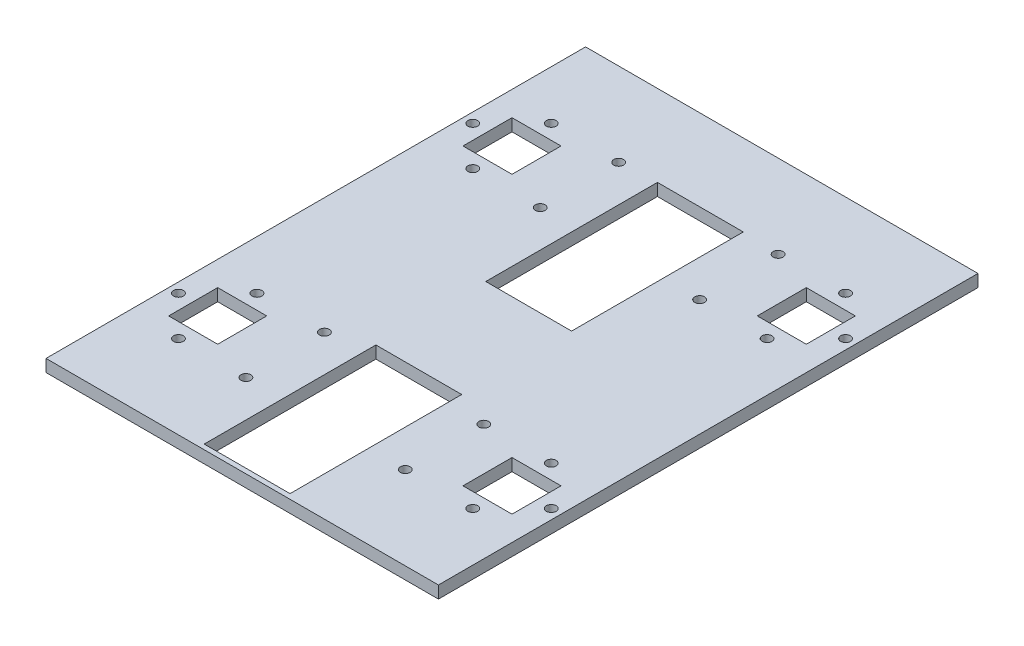
SolidWorks part; units mm, degrees
other "Markup1"
sketch "Sketch4" plane through (-101.6, 6.35, 139.7) normal (-0.0746, 0.7649, 0.6399) x (0.9963, 0.0292, 0.0813)
material "Balsa"
ref_plane "Front Plane" through (0, 0, 0) normal (0, 0, 1) x (1, 0, 0)
ref_plane "Top Plane" through (0, 0, 0) normal (0, 1, 0) x (1, 0, 0)
ref_plane "Right Plane" through (0, 0, 0) normal (1, 0, 0) x (0, 0, -1)
sketch "Sketch1" plane through (0, 0, 0) normal (0, 1, 0) x (1, 0, 0)
  line L1 (-101.6, 139.7) -> (101.6, 139.7)
  line L2 (-101.6, 139.7) -> (-101.6, -139.7)
  line L3 (-101.6, -139.7) -> (101.6, -139.7)
  line L4 (101.6, 139.7) -> (101.6, -139.7)
  line L5 (-101.6, 139.7) -> (101.6, -139.7) construction
  line L6 (-101.6, -139.7) -> (101.6, 139.7) construction
  point P0 (0, 0)
  dimension "D1" = 279.4
  dimension "D2" = 203.2
extrude "Boss-Extrude1" add sketch "Sketch1" along normal blind 6.35
sketch "Sketch2" plane through (0, 6.35, 0) normal (0, 1, 0) x (1, 0, 0)
  line L0 (-101.6, 139.7) -> (-101.6, -139.7) construction
  line L1 (-88.9, 88.9) -> (-63.5, 88.9)
  line L2 (-88.9, 88.9) -> (-88.9, 63.5)
  line L3 (-88.9, 63.5) -> (-63.5, 63.5)
  line L4 (-63.5, 88.9) -> (-63.5, 63.5)
  line L5 (-88.9, 88.9) -> (-63.5, 63.5) construction
  line L6 (-88.9, 63.5) -> (-63.5, 88.9) construction
  line L7 (101.6, 139.7) -> (-101.6, 139.7) construction
  line L8 (-76.2, 76.2) -> (-31.4633, 76.2) construction
  line L9 (-76.2, 55.88) -> (-7.5803, 55.88) construction
  line L10 (-76.2, 76.2) -> (-76.2, 32.693) construction
  circle A4 centre (-41.275, 55.88) radius 2.54
  circle A5 centre (-41.275, 96.52) radius 2.54
  circle A6 centre (-76.2, 55.88) radius 2.54
  circle A7 centre (-96.52, 76.2) radius 2.54
  circle A8 centre (-76.2, 96.52) radius 2.54
  circle A9 centre (-55.88, 76.2) radius 2.54 [skipped]
  point P0 (-76.2, 76.2)
  point P22 (-76.2, 76.2)
  point P30 (-76.2, 76.2)
  dimension "D4" = 5.08
  dimension "D5" = 7.62
  dimension "D7" = 5.08
  dimension "D1" = 12.7
  dimension "D2" = 50.8
  dimension "D3" = 25.4
  dimension "D8" = 34.925
  dimension "D6" = 4
extrude "Cut-Extrude1" cut sketch "Sketch2" against normal through all both and the other way through all
mirror "Mirror1" about plane through (0, 0, 0) normal (0, 0, 1) of "Cut-Extrude1"
mirror "Mirror2" about plane through (0, 0, 0) normal (1, 0, 0) of "Mirror1", "Cut-Extrude1"
sketch "Sketch3" plane through (32.7636, 6.35, -4.6112) normal (0, 1, 0) x (0, 0, 1)
  line L0 (29.3894, -32.7636) -> (-71.5888, -32.7636) construction
  line L1 (-92.0984, -20.9049) -> (-74.2352, -17.7551)
  line L2 (-92.0984, -44.6223) -> (-74.2352, -47.7721)
  line L3 (-92.9248, -21.8897) -> (-92.9248, -43.6375)
  line L4 (-71.5888, 30.7364) -> (-71.5888, -96.2636) construction
  line L5 (-58.8888, 30.7364) -> (-84.2888, 30.7364) construction
  line L6 (-58.8888, -96.2636) -> (-84.2888, -96.2636) construction
  line L8 (-92.9248, -54.9886) -> (-4.0248, -54.9886)
  line L9 (-92.9248, -54.9886) -> (-92.9248, -10.5386)
  line L10 (-92.9248, -10.5386) -> (-4.0248, -10.5386)
  line L11 (-4.0248, -54.9886) -> (-4.0248, -10.5386)
  line L12 (141.7712, -54.9886) -> (52.8712, -54.9886)
  line L13 (141.7712, -54.9886) -> (141.7712, -10.5386)
  line L14 (141.7712, -10.5386) -> (52.8712, -10.5386)
  line L15 (52.8712, -54.9886) -> (52.8712, -10.5386)
  line L16 (141.7712, -54.9886) -> (52.8712, -10.5386) construction
  line L17 (141.7712, -10.5386) -> (52.8712, -54.9886) construction
  arc A0 (-74.2352, -47.7721) -> (-74.2352, -17.7551) centre (-71.5888, -32.7636) ccw
  circle A1 centre (-71.5888, -32.7636) radius 9.906 construction
  arc A2 (-92.9248, -43.6375) -> (-92.0984, -44.6223) centre (-91.9248, -43.6375) ccw
  arc A3 (-92.9248, -21.8897) -> (-92.0984, -20.9049) centre (-91.9248, -21.8897) cw
  point P12 (-92.9248, -32.7636)
  point P13 (-11.6448, -32.7636)
  point P14 (-56.3488, -32.7636)
  point P24 (-4.0248, -32.7636)
  point P25 (97.3212, -32.7636)
  point P30 (0, 0)
  dimension "D1" = 30.48
  dimension "D2" = 19.812
  dimension "D3" = 1
  dimension "D4" = 81.28
  dimension "D5" = 36.576
  dimension "D6" = 10
  dimension "D7" = 44.45
  dimension "D8" = 88.9
  dimension "D9" = 88.9
  dimension "D10" = 44.45
  dimension "D11" = 56.896
extrude "Cut-Extrude2" cut sketch "Sketch3" against normal through all both and the other way through all contours L9 A3 L1 A0 L2 A2 L8 L11 L10 | L13 L12 L15 L14
